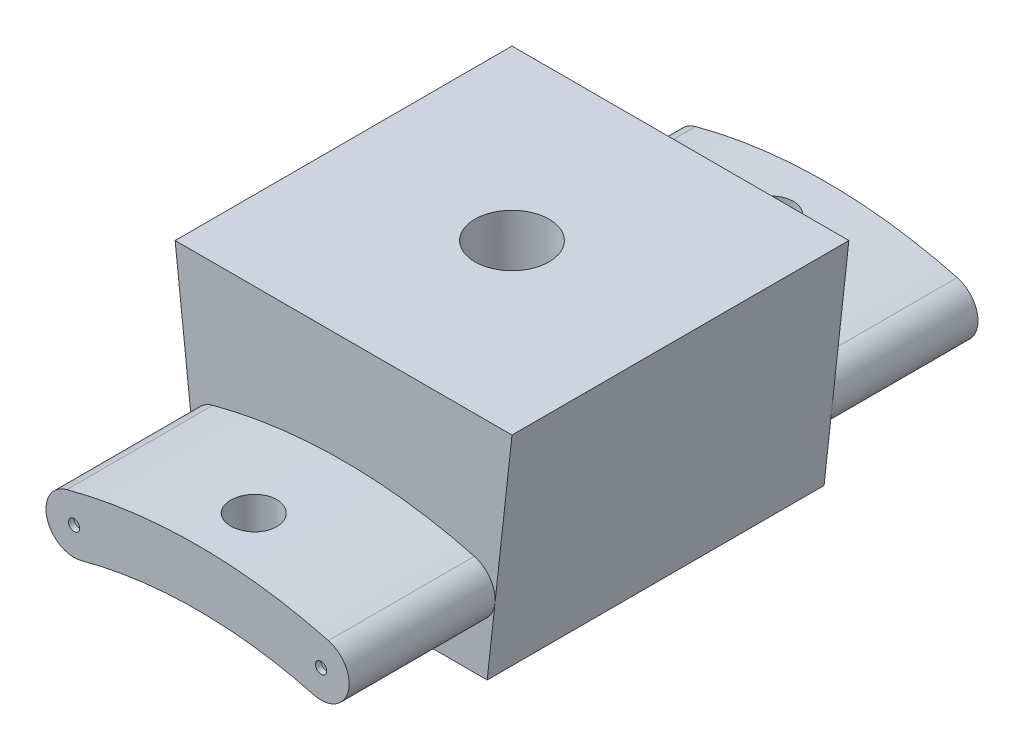
SolidWorks part; units mm, degrees
material "7075-T6 (SN)"
ref_plane "Front Plane" through (0, 0, 0) normal (0, 0, 1) x (1, 0, 0)
ref_plane "Top Plane" through (0, 0, 0) normal (0, 1, 0) x (1, 0, 0)
ref_plane "Right Plane" through (0, 0, 0) normal (1, 0, 0) x (0, 0, -1)
sketch "Sketch1" plane through (0, 0, 0) normal (0, 1, 0) x (1, 0, 0)
  line L1 (-7.5, -7.5) -> (7.5, -7.5)
  line L2 (-7.5, -7.5) -> (-7.5, 7.5)
  line L3 (-7.5, 7.5) -> (7.5, 7.5)
  line L4 (7.5, -7.5) -> (7.5, 7.5)
  line L5 (-7.5, -7.5) -> (7.5, 7.5) construction
  line L6 (-7.5, 7.5) -> (7.5, -7.5) construction
  point P0 (0, 0)
  dimension "D1" = 15
extrude "Boss-Extrude1" add sketch "Sketch1" along normal blind 10
sketch "Sketch2" plane through (0, 0, 0) normal (0, -1, 0) x (1, 0, 0)
  circle A0 centre (0, 0) radius 6
  dimension "D1" = 12
extrude "Cut-Extrude1" cut sketch "Sketch2" against normal blind 4
sketch "Sketch3" plane through (0, 4, 0) normal (0, -1, 0) x (1, 0, 0)
  circle A0 centre (0, 0) radius 5
  dimension "D1" = 10
extrude "Cut-Extrude2" cut sketch "Sketch3" against normal blind 3.5
sketch "Sketch4" plane through (0, 0, 7.5) normal (0, 0, 1) x (1, 0, 0)
  line L0 (-7.5, 0) -> (7.5, 0) construction
  arc A0 (5.4999, 3.2759) -> (-5.4999, 3.2759) centre (0, -17.25) ccw construction
  arc A1 (5.8234, 4.4833) -> (-5.8234, 4.4833) centre (0, -17.25) ccw
  arc A2 (5.1764, 2.0685) -> (-5.1764, 2.0685) centre (0, -17.25) ccw
  arc A3 (5.1764, 2.0685) -> (5.8234, 4.4833) centre (5.4999, 3.2759) ccw
  arc A4 (-5.8234, 4.4833) -> (-5.1764, 2.0685) centre (-5.4999, 3.2759) ccw
  point P3 (0, 4)
  dimension "D1" = 2.5
  dimension "D2" = 20
  dimension "D3" = 4
  dimension "D4" = 30
extrude "Boss-Extrude2" add sketch "Sketch4" along normal blind 6.5
mirror "Mirror1" about plane through (0, 0, 0) normal (0, 0, 1) of "Boss-Extrude2"
hole_wizard "M4 Tapped Hole1" positions "Sketch6" profile "Sketch7" tap size "M4" standard "DIN" end condition up to next
sketch "Sketch6" plane through (0, 10, 0) normal (0, 1, 0) x (1, 0, 0)
  point P0 (0, 0)
sketch "Sketch7" plane through (0, 10, 0) normal (1, 0, 0) x (0, 0, 1)
  line L0 (0, 0) -> (0, 2.5)
  line L1 (0, 2.5) -> (1.65, 2.5)
  line L2 (1.65, 2.5) -> (1.65, 0)
  line L5 (1.65, 0) -> (0, 0)
  line L11 (0, -6.35) -> (0, 107.95) construction
  dimension "Thru Tap Drill Dia." = 3.3
  dimension "Thru Tap Drill Depth" = 2.5
cosmetic thread "Hole Thread1" parameters "D2"=4
hole_wizard "M2.5 Tapped Hole1" positions "Sketch8" profile "Sketch9" tap size "M2.5" standard "DIN"
sketch "Sketch8" plane through (0, 10, 0) normal (0, 1, 0) x (1, 0, 0)
  line L0 (0, 11.5) -> (0, -11.5) construction
  line L2 (5.8234, 14) -> (-5.8234, 14) construction
  point P0 (0, 11.5)
  point P2 (0, -11.5)
  dimension "D1" = 2.5
sketch "Sketch9" plane through (0, 10, -11.5) normal (1, 0, 0) x (0, 0, 1)
  line L0 (0, 0) -> (0, 7.25)
  line L1 (0, 7.25) -> (1.025, 7.25)
  line L2 (1.025, 7.25) -> (1.025, 0)
  line L5 (1.025, 0) -> (0, 0)
  line L11 (0, -6.35) -> (0, 107.95) construction
  dimension "Thru Tap Drill Dia." = 2.05
  dimension "Thru Tap Drill Depth" = 7.25
cosmetic thread "Hole Thread2" parameters "D2"=2.5
cosmetic thread "Hole Thread3" parameters "D2"=2.5
sketch "Sketch10" plane through (0, 0, 14) normal (0, 0, 1) x (1, 0, 0)
  circle A1 centre (-5.4999, 3.2759) radius 0.25
  circle A2 centre (5.4999, 3.2759) radius 0.25
  arc A3 (-5.8234, 4.4833) -> (-5.1764, 2.0685) centre (-5.4999, 3.2759) ccw construction
  arc A4 (5.1764, 2.0685) -> (5.8234, 4.4833) centre (5.4999, 3.2759) ccw construction
  dimension "D1" = 0.5
extrude "Cut-Extrude3" cut sketch "Sketch10" against normal blind 0.25
sketch "Sketch11" plane through (0, 0, 7.5) normal (0, 0, 1) x (1, 0, 0)
  line L0 (-7.5, 10) -> (-6.3958, 0)
  line L1 (-7.5, 0) -> (7.5, 0) construction
  line L2 (-6.3958, 0) -> (-7.5, 0)
  line L3 (-7.5, 0) -> (-7.5, 10)
  line L4 (7.5, 10) -> (6.3958, 0)
  line L5 (6.3958, 0) -> (7.5, 0)
  line L6 (7.5, 0) -> (7.5, 10)
  arc A0 (-5.8234, 4.4833) -> (-5.1764, 2.0685) centre (-5.4999, 3.2759) ccw construction
extrude "Cut-Extrude4" cut sketch "Sketch11" against normal up to next
